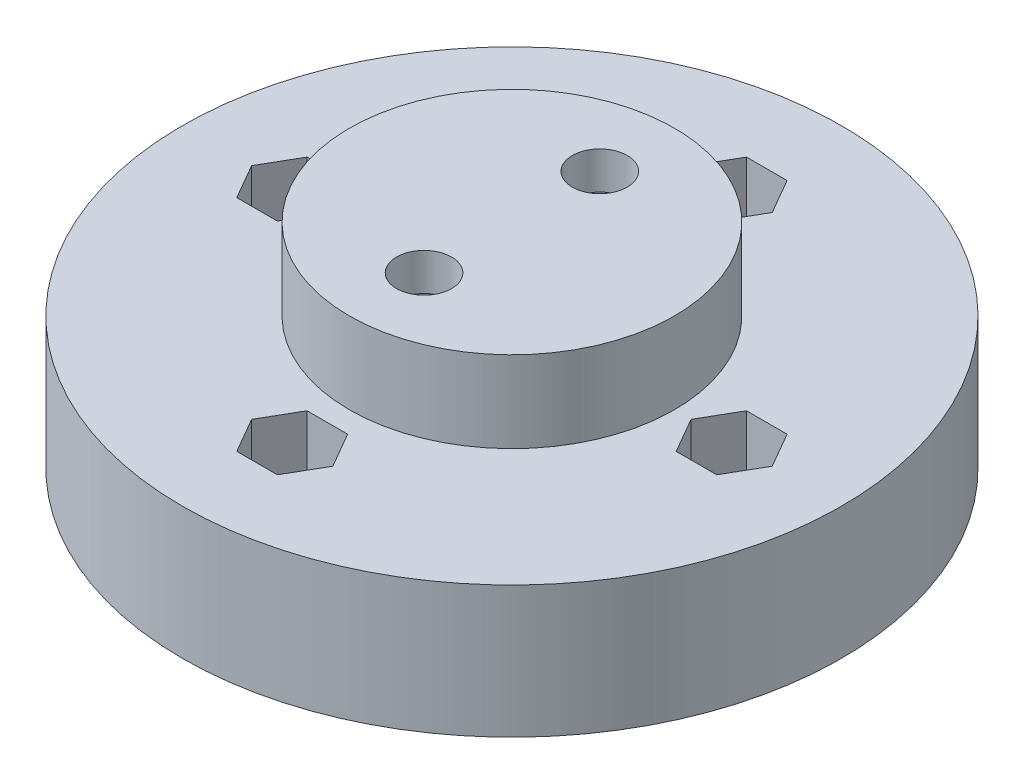
SolidWorks part; units mm, degrees
ref_plane "Front Plane" through (0, 0, 0) normal (0, 0, 1) x (1, 0, 0)
ref_plane "Top Plane" through (0, 0, 0) normal (0, 1, 0) x (1, 0, 0)
ref_plane "Right Plane" through (0, 0, 0) normal (1, 0, 0) x (0, 0, -1)
sketch "Sketch1" plane through (0, 0, 0) normal (0, 1, 0) x (1, 0, 0)
  circle A0 centre (0, 0) radius 19.05
  dimension "D1" = 38.1
extrude "Boss-Extrude1" add sketch "Sketch1" along normal blind 7.62
sketch "Sketch2" plane through (0, 7.62, 0) normal (0, 1, 0) x (1, 0, 0)
  circle A0 centre (0, 0) radius 9.398
  dimension "D1" = 18.796
extrude "Boss-Extrude2" add sketch "Sketch2" along normal blind 4.699
sketch "Sketch7" plane through (0, 0, 0) normal (0, -1, 0) x (1, 0, 0)
  circle A0 centre (0, 5.08) radius 2.921
  circle A1 centre (0, -5.08) radius 2.921
  dimension "D1" = 5.842
  dimension "D2" = 5.842
  dimension "D3" = 5.08
  dimension "D4" = 10.16
extrude "Cut-Extrude5" cut sketch "Sketch7" against normal blind 10.16
sketch "Sketch12" plane through (0, 10.16, 0) normal (0, -1, 0) x (1, 0, 0)
  circle A0 centre (0, 5.08) radius 1.5875
  circle A1 centre (0, -5.08) radius 1.5875
  circle A2 centre (0, -5.08) radius 2.921 construction
  circle A3 centre (0, 5.08) radius 2.921 construction
  dimension "D1" = 3.175
  dimension "D2" = 3.175
extrude "Cut-Extrude6" cut sketch "Sketch12" against normal through all
sketch "Sketch13" plane through (0, 7.62, 0) normal (0, 1, 0) x (1, 0, 0)
  line L1 (2.3464, 12.7) -> (1.1732, 14.732)
  line L2 (1.1732, 14.732) -> (-1.1732, 14.732)
  line L3 (-1.1732, 14.732) -> (-2.3464, 12.7)
  line L4 (-2.3464, 12.7) -> (-1.1732, 10.668)
  line L5 (-1.1732, 10.668) -> (1.1732, 10.668)
  line L6 (1.1732, 10.668) -> (2.3464, 12.7)
  line L7 (2.3464, -12.7) -> (1.1732, -10.668)
  line L8 (1.1732, -10.668) -> (-1.1732, -10.668)
  line L9 (-1.1732, -10.668) -> (-2.3464, -12.7)
  line L10 (-2.3464, -12.7) -> (-1.1732, -14.732)
  line L11 (-1.1732, -14.732) -> (1.1732, -14.732)
  line L12 (1.1732, -14.732) -> (2.3464, -12.7)
  line L13 (15.0464, 0) -> (13.8732, 2.032)
  line L14 (13.8732, 2.032) -> (11.5268, 2.032)
  line L15 (11.5268, 2.032) -> (10.3536, 0)
  line L16 (10.3536, 0) -> (11.5268, -2.032)
  line L17 (11.5268, -2.032) -> (13.8732, -2.032)
  line L18 (13.8732, -2.032) -> (15.0464, 0)
  line L19 (-10.3536, 0) -> (-11.5268, 2.032)
  line L20 (-11.5268, 2.032) -> (-13.8732, 2.032)
  line L21 (-13.8732, 2.032) -> (-15.0464, 0)
  line L22 (-15.0464, 0) -> (-13.8732, -2.032)
  line L23 (-13.8732, -2.032) -> (-11.5268, -2.032)
  line L24 (-11.5268, -2.032) -> (-10.3536, 0)
  circle A0 centre (0, 12.7) radius 2.032 construction
  circle A1 centre (0, -12.7) radius 2.032 construction
  circle A2 centre (12.7, 0) radius 2.032 construction
  circle A3 centre (-12.7, 0) radius 2.032 construction
  point P34 (0, 0)
  dimension "D1" = 4.064
  dimension "D2" = 4.064
  dimension "D3" = 4.064
  dimension "D4" = 4.064
  dimension "D5" = 25.4
  dimension "D6" = 25.4
  dimension "D7" = 12.7
  dimension "D8" = 12.7
extrude "Cut-Extrude7" cut sketch "Sketch13" against normal blind 5.08
sketch "Sketch14" plane through (0, 7.62, 0) normal (0, 1, 0) x (1, 0, 0)
  circle A0 centre (0, 12.7) radius 1.27
  circle A1 centre (12.7, 0) radius 1.27
  circle A2 centre (0, -12.7) radius 1.27
  circle A3 centre (-12.7, 0) radius 1.27
  dimension "D5" = 2.54
  dimension "D1" = 25.4
  dimension "D2" = 12.7
  dimension "D3" = 25.4
  dimension "D4" = 12.7
extrude "Cut-Extrude8" cut sketch "Sketch14" against normal through all
